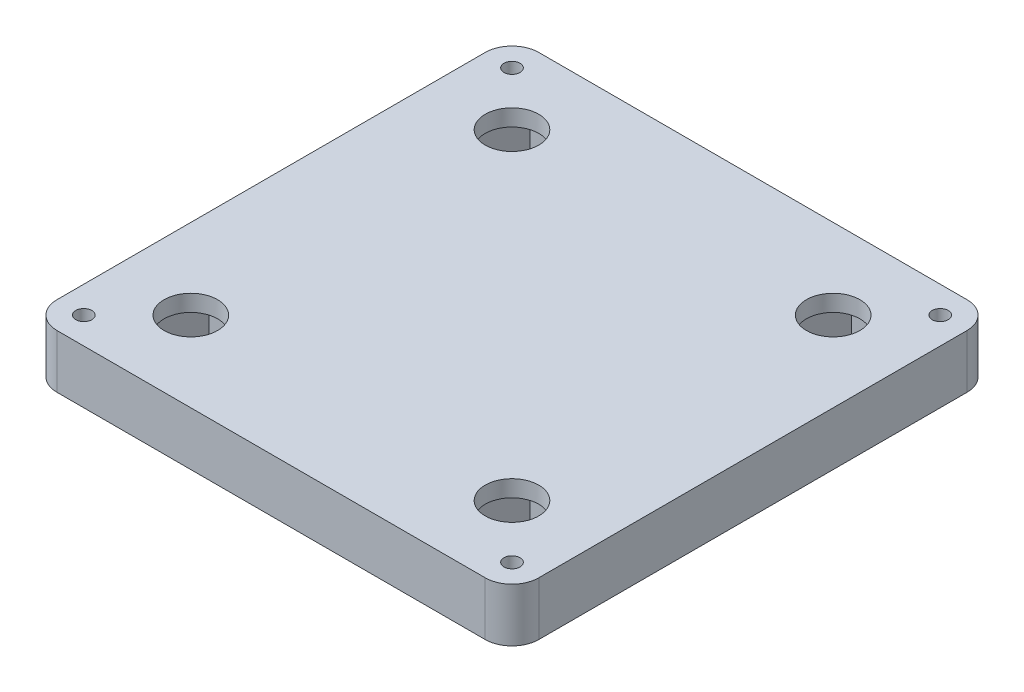
SolidWorks part; units mm, degrees
ref_plane "Front" through (0, 0, 0) normal (0, 0, 1) x (1, 0, 0)
ref_plane "Top" through (0, 0, 0) normal (0, 1, 0) x (1, 0, 0)
ref_plane "Right" through (0, 0, 0) normal (1, 0, 0) x (0, 0, -1)
sketch "Sketch1" plane through (0, 0, 0) normal (0, 1, 0) x (1, 0, 0)
  line L1 (-45, 45) -> (45, 45)
  line L2 (-45, 45) -> (-45, -45)
  line L3 (-45, -45) -> (45, -45)
  line L4 (45, 45) -> (45, -45)
  line L5 (-45, 45) -> (45, -45) construction
  line L6 (-45, -45) -> (45, 45) construction
  point P0 (0, 0)
  dimension "D1" = 90
extrude "Boss-Extrude1" add sketch "Sketch1" along normal blind 10
sketch "Sketch2" plane through (0, 0, 0) normal (0, -1, 0) x (1, 0, 0)
  line L1 (9.2376, 0) -> (4.6188, 8)
  line L2 (4.6188, 8) -> (-4.6188, 8)
  line L3 (-4.6188, 8) -> (-9.2376, 0)
  line L4 (-9.2376, 0) -> (-4.6188, -8)
  line L5 (-4.6188, -8) -> (4.6188, -8)
  line L6 (4.6188, -8) -> (9.2376, 0)
  line L12 (-45, 45) -> (45, -45) construction
  line L19 (-15.2868, 8.7548) -> (-8.7548, 15.2868)
  line L20 (-8.7548, 15.2868) -> (-11.1457, 24.2096)
  line L21 (-11.1457, 24.2096) -> (-20.0685, 26.6005)
  line L22 (-20.0685, 26.6005) -> (-26.6005, 20.0685)
  line L23 (-26.6005, 20.0685) -> (-24.2096, 11.1457)
  line L24 (-24.2096, 11.1457) -> (-15.2868, 8.7548)
  line L25 (20.0685, -26.6005) -> (26.6005, -20.0685)
  line L26 (26.6005, -20.0685) -> (24.2096, -11.1457)
  line L27 (24.2096, -11.1457) -> (15.2868, -8.7548)
  line L28 (15.2868, -8.7548) -> (8.7548, -15.2868)
  line L29 (8.7548, -15.2868) -> (11.1457, -24.2096)
  line L30 (11.1457, -24.2096) -> (20.0685, -26.6005)
  line L31 (-45, -45) -> (-45, 45) construction
  line L32 (45, 45) -> (45, -45) construction
  line L33 (45, -45) -> (-45, -45) construction
  line L34 (-45, 45) -> (45, 45) construction
  circle A0 centre (0, 0) radius 8 construction
  arc A1 (17.6777, -17.6777) -> (-17.6777, 17.6777) centre (0, 0) ccw construction
  arc A2 (23.3345, -23.3345) -> (-23.3345, 23.3345) centre (0, 0) ccw
  arc A3 (12.0208, -12.0208) -> (-12.0208, 12.0208) centre (0, 0) ccw
  arc A4 (12.0208, -12.0208) -> (23.3345, -23.3345) centre (17.6777, -17.6777) ccw
  arc A5 (-23.3345, 23.3345) -> (-12.0208, 12.0208) centre (-17.6777, 17.6777) ccw
  circle A6 centre (-17.6777, 17.6777) radius 8 construction
  circle A7 centre (17.6777, -17.6777) radius 8 construction
  point P11 (17.6777, 17.6777)
  dimension "D2" = 25
  dimension "D3" = 8
  dimension "D1" = 16
extrude "Cut-Extrude1" cut sketch "Sketch2" against normal blind 6.9 contours L5 L6 L1 L2 L3 L4 | A3 L28 L27 L26 A2 L21 L20 L19 | L28 A4 A2 L26 L27 | A2 A5 L19 L20 L21 | A5 L22 L23 | A5 L24 L19 | A5 L23 L24 | A4 L28 L29 | A4 L29 L30 | A4 L30 L25
sketch "Sketch3" plane through (0, 10, 0) normal (0, 1, 0) x (1, 0, 0)
  line L1 (-40, -40) -> (40, -40) construction
  line L2 (-40, -40) -> (-40, 40) construction
  line L3 (-40, 40) -> (40, 40) construction
  line L4 (40, -40) -> (40, 40) construction
  line L5 (-40, -40) -> (40, 40) construction
  line L6 (-40, 40) -> (40, -40) construction
  circle A0 centre (-40, 40) radius 1.5
  circle A1 centre (40, 40) radius 1.5
  circle A2 centre (40, -40) radius 1.5
  circle A3 centre (-40, -40) radius 1.5
  point P0 (0, 0)
  dimension "D2" = 3
  dimension "D1" = 80
extrude "Cut-Extrude2" cut sketch "Sketch3" against normal through all
sketch "Sketch4" plane through (0, 10, 0) normal (0, 1, 0) x (1, 0, 0)
  line L1 (-30, -30) -> (30, -30) construction
  line L2 (-30, -30) -> (-30, 30) construction
  line L3 (-30, 30) -> (30, 30) construction
  line L4 (30, -30) -> (30, 30) construction
  line L5 (-30, -30) -> (30, 30) construction
  line L6 (-30, 30) -> (30, -30) construction
  circle A0 centre (-30, 30) radius 5
  circle A1 centre (30, 30) radius 5
  circle A2 centre (30, -30) radius 5
  circle A3 centre (-30, -30) radius 5
  point P0 (0, 0)
  dimension "D2" = 10
  dimension "D1" = 60
extrude "Cut-Extrude3" cut sketch "Sketch4" against normal through all
sketch "Sketch6" plane through (0, 0, 0) normal (0, -1, 0) x (1, 0, 0)
  line L1 (-25.3812, 22) -> (-20.7624, 30)
  line L2 (-20.7624, 30) -> (-25.3812, 38)
  line L3 (-25.3812, 38) -> (-34.6188, 38)
  line L4 (-34.6188, 38) -> (-39.2376, 30)
  line L5 (-39.2376, 30) -> (-34.6188, 22)
  line L6 (-34.6188, 22) -> (-25.3812, 22)
  line L7 (34.6188, 22) -> (39.2376, 30)
  line L8 (39.2376, 30) -> (34.6188, 38)
  line L9 (34.6188, 38) -> (25.3812, 38)
  line L10 (25.3812, 38) -> (20.7624, 30)
  line L11 (20.7624, 30) -> (25.3812, 22)
  line L12 (25.3812, 22) -> (34.6188, 22)
  line L13 (34.6188, -38) -> (39.2376, -30)
  line L14 (39.2376, -30) -> (34.6188, -22)
  line L15 (34.6188, -22) -> (25.3812, -22)
  line L16 (25.3812, -22) -> (20.7624, -30)
  line L17 (20.7624, -30) -> (25.3812, -38)
  line L18 (25.3812, -38) -> (34.6188, -38)
  line L19 (-20.7624, -30) -> (-25.3812, -22)
  line L20 (-25.3812, -22) -> (-34.6188, -22)
  line L21 (-34.6188, -22) -> (-39.2376, -30)
  line L22 (-39.2376, -30) -> (-34.6188, -38)
  line L23 (-34.6188, -38) -> (-25.3812, -38)
  line L24 (-25.3812, -38) -> (-20.7624, -30)
  circle A0 centre (-30, 30) radius 8 construction
  circle A1 centre (30, 30) radius 8 construction
  circle A2 centre (30, -30) radius 8 construction
  circle A3 centre (-30, -30) radius 8 construction
  dimension "D1" = 16
extrude "Cut-Extrude4" cut sketch "Sketch6" against normal blind 6.9
fillet "Fillet1" radius 5 4 edges at (-45, 5, 45) (-45, 5, -45) (45, 5, 45) (45, 5, -45)
